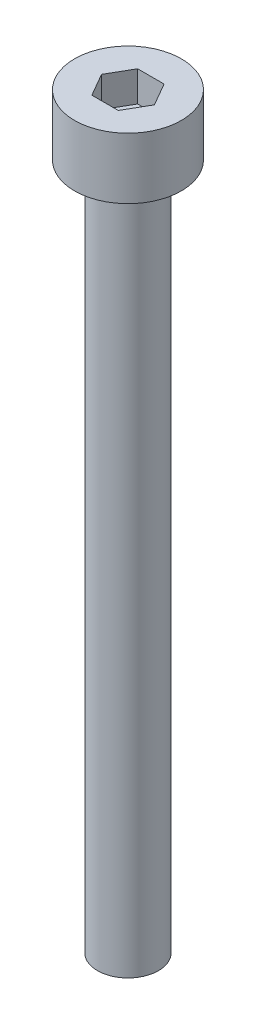
SolidWorks part; units mm, degrees
material "AISI 304"
ref_plane "前视基准面" through (0, 0, 0) normal (0, 0, 1) x (1, 0, 0)
ref_plane "上视基准面" through (0, 0, 0) normal (0, 1, 0) x (1, 0, 0)
ref_plane "右视基准面" through (0, 0, 0) normal (1, 0, 0) x (0, 0, -1)
sketch "草图1" plane through (0, 0, 0) normal (0, 1, 0) x (1, 0, 0)
  circle A0 centre (0, 0) radius 3.5
  dimension "D1" = 7
extrude "杯头" add sketch "草图1" along normal blind 4
sketch "草图2" plane through (0, 4, 0) normal (0, 1, 0) x (1, 0, 0)
  line L1 (1.7321, 0) -> (0.866, 1.5)
  line L2 (0.866, 1.5) -> (-0.866, 1.5)
  line L3 (-0.866, 1.5) -> (-1.7321, 0)
  line L4 (-1.7321, 0) -> (-0.866, -1.5)
  line L5 (-0.866, -1.5) -> (0.866, -1.5)
  line L6 (0.866, -1.5) -> (1.7321, 0)
  circle A0 centre (0, 0) radius 1.5 construction
  dimension "D1" = 3
extrude "内六角口" cut sketch "草图2" against normal blind 2
sketch "草图3" plane through (0, 0, 0) normal (0, -1, 0) x (1, 0, 0)
  circle A0 centre (0, 0) radius 2
  dimension "D1" = 4
extrude "螺纹长度" add sketch "草图3" along normal blind 45
